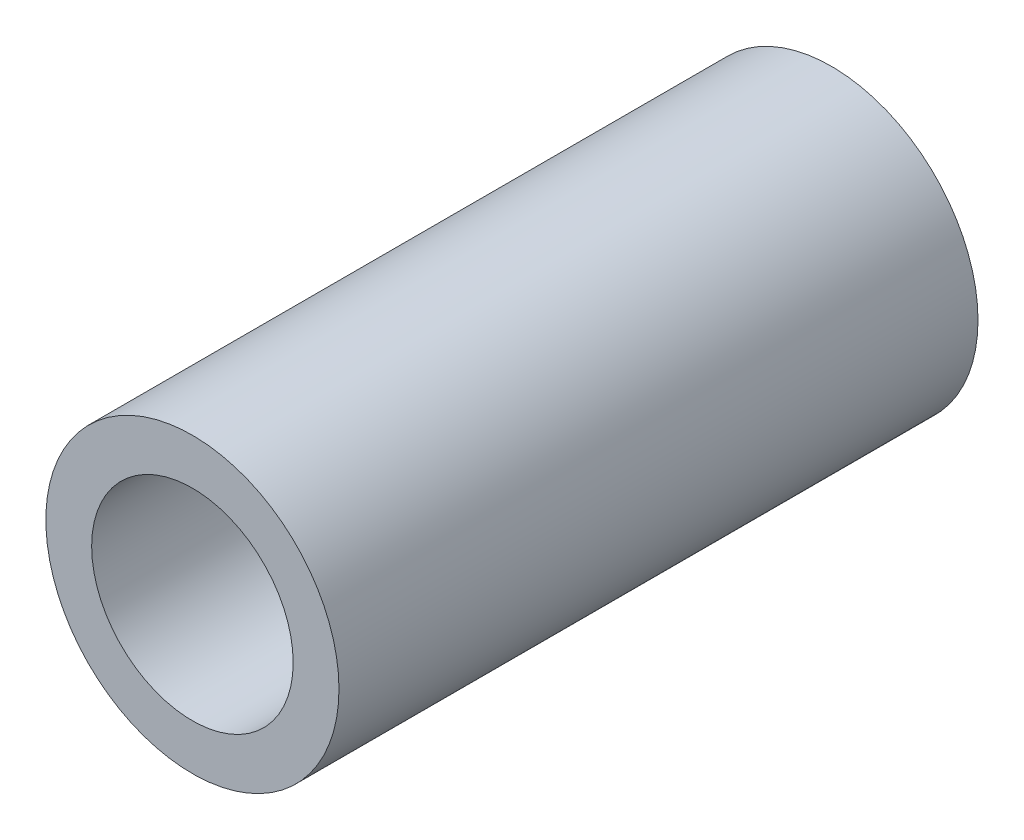
SolidWorks part; units mm, degrees
ref_plane "正面" through (0, 0, 0) normal (0, 0, 1) x (1, 0, 0)
ref_plane "平面" through (0, 0, 0) normal (0, 1, 0) x (1, 0, 0)
ref_plane "右側面" through (0, 0, 0) normal (1, 0, 0) x (0, 0, -1)
sketch "ｽｹｯﾁ1" plane through (0, 0, 0) normal (0, 0, 1) x (1, 0, 0)
  circle A0 centre (0, 0) radius 2.75
  circle A1 centre (0, 0) radius 4
  dimension "D1" = 5.5
  dimension "D2" = 8
extrude "ﾎﾞｽ - 押し出し1" add sketch "ｽｹｯﾁ1" along normal blind 17.44
